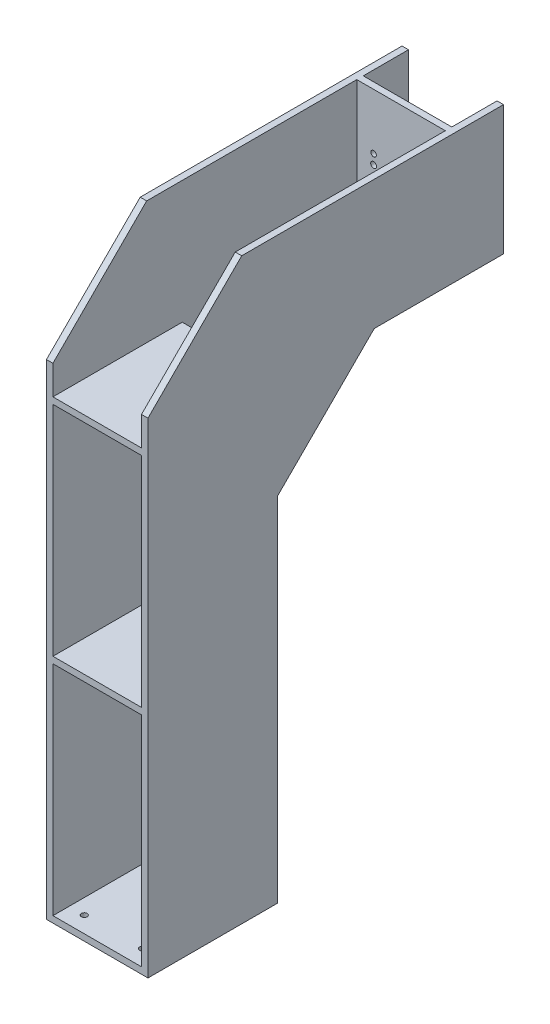
SolidWorks part; units mm, degrees
material "3003 Alloy"
ref_plane "Front Plane" through (0, 0, 0) normal (0, 0, 1) x (1, 0, 0)
ref_plane "Top Plane" through (0, 0, 0) normal (0, 1, 0) x (1, 0, 0)
ref_plane "Right Plane" through (0, 0, 0) normal (1, 0, 0) x (0, 0, -1)
sketch "Sketch1" plane through (0, 0, 0) normal (1, 0, 0) x (0, 0, -1)
  line L0 (0, 0) -> (0, 750)
  line L1 (0, 750) -> (145, 895)
  line L2 (145, 895) -> (550, 895)
  line L3 (550, 895) -> (550, 695)
  line L6 (200, 0) -> (0, 0)
  line L11 (200, 0) -> (200, 695)
  line L12 (200, 695) -> (550, 695)
  line L13 (200, 545) -> (350, 695)
  dimension "D1" = 200
  dimension "D2" = 895
  dimension "D3" = 750
  dimension "D4" = 200
  dimension "D5" = 550
  dimension "D6" = 45
  dimension "D7" = 45
  dimension "D8" = 150
extrude "Boss-Extrude1" add sketch "Sketch1" along normal blind 10 and the other way blind 147 contours L11 L13 L12 | L11 L12 L3 L2 L1 L0 L6
sketch "Sketch3" plane through (0, 895, 0) normal (0, 1, 0) x (1, 0, 0)
  line L0 (-147, 550) -> (10, 550) construction
  line L1 (-137, 550) -> (0, 550)
  line L2 (-137, 550) -> (-137, 0)
  line L3 (-137, 0) -> (0, 0)
  line L4 (0, 550) -> (0, 0)
  line L5 (-147, 0) -> (10, 0) construction
  point P8 (-68.5, 550)
  point P9 (-68.5, 550)
  dimension "D1" = 137
extrude "Cut-Extrude1" cut sketch "Sketch3" against normal offset from surface (885 mm away) 10 up to face at (-68.5, 0, -100)
ref_plane "Plane1" through (0, 0, -480) normal (0, 0, -1) x (-1, 0, 0)
sketch "Sketch4" plane through (0, 0, -480) normal (0, 0, -1) x (-1, 0, 0)
  line L1 (0, 895) -> (137, 895)
  line L2 (0, 895) -> (0, 695)
  line L3 (0, 695) -> (137, 695)
  line L4 (137, 895) -> (137, 695)
extrude "Boss-Extrude2" add sketch "Sketch4" against normal blind 10 contours L2 L1 L4 L3
sketch "Sketch6" plane through (0, 0, -470) normal (0, 0, 1) x (1, 0, 0)
  line L0 (0, 695) -> (-137, 695) construction
  line L1 (-111, 747.2) -> (-26, 747.2) construction
  line L2 (0, 895) -> (-137, 895) construction
  line L3 (0, 895) -> (0, 695) construction
  circle A0 centre (-111, 747.2) radius 4.5
  circle A1 centre (-26, 747.2) radius 4.5
  circle A2 centre (-111, 793.7) radius 4.5
  circle A3 centre (-26, 793.7) radius 4.5
  circle A4 centre (-63, 788.5) radius 8
  circle A5 centre (-111, 808.7) radius 4.25
  circle A6 centre (-26, 732.2) radius 4.25
  point P10 (-68.5, 895)
  point P11 (-68.5, 747.2)
  dimension "D3" = 9
  dimension "D5" = 16
  dimension "D8" = 8.5
  dimension "D1" = 52.2
  dimension "D2" = 85
  dimension "D4" = 46.5
  dimension "D6" = 93.5
  dimension "D7" = 63
  dimension "D9" = 15
  dimension "D10" = 15
extrude "Cut-Extrude3" cut sketch "Sketch6" against normal up to next
ref_plane "Plane2" through (0, 705, 0) normal (0, -1, 0) x (-1, 0, 0)
sketch "Sketch8" plane through (0, 705, 0) normal (0, -1, 0) x (-1, 0, 0)
  line L1 (-10, 0) -> (147, 0)
  line L2 (-10, 0) -> (-10, 200)
  line L3 (-10, 200) -> (147, 200)
  line L4 (147, 0) -> (147, 200)
extrude "Boss-Extrude3" add sketch "Sketch8" along normal blind 10
pattern_linear "LPattern1" count 3 spacing 347.5 along (0, -1, 0) of "Boss-Extrude3"
sketch "Sketch7" plane through (0, 10, 0) normal (0, 1, 0) x (1, 0, 0)
  line L1 (-113.5, 25) -> (-23.5, 25) construction
  line L2 (-23.5, 25) -> (-23.5, 175) construction
  line L3 (0, 0) -> (0, 200) construction
  line L4 (-137, 0) -> (0, 0) construction
  circle A0 centre (-113.5, 175) radius 4.5
  circle A1 centre (-23.5, 175) radius 4.5
  circle A2 centre (-23.5, 25) radius 4.5
  circle A3 centre (-113.5, 25) radius 4.5
  circle A4 centre (-113.5, 155) radius 4.25
  circle A5 centre (-23.5, 45) radius 4.25
  point P14 (0, 100)
  point P15 (-23.5, 100)
  point P18 (-68.5, 0)
  point P19 (-68.5, 25)
  dimension "D1" = 8.5
  dimension "D2" = 9
  dimension "D3" = 90
  dimension "D4" = 150
  dimension "D5" = 20
  dimension "D6" = 20
extrude "Cut-Extrude4" cut sketch "Sketch7" against normal up to next
